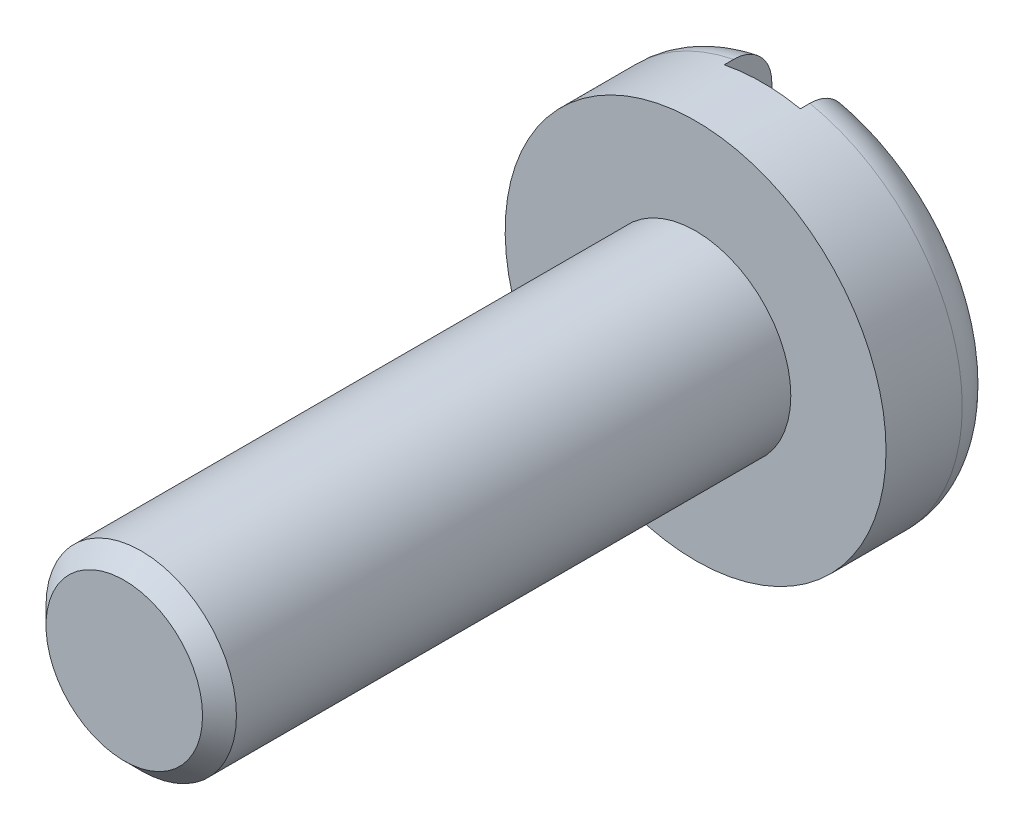
SolidWorks part; units mm, degrees
material "Сталь"
ref_plane "Спереди" through (0, 0, 0) normal (0, 0, 1) x (1, 0, 0)
ref_plane "Сверху" through (0, 0, 0) normal (0, 1, 0) x (1, 0, 0)
ref_plane "Справа" through (0, 0, 0) normal (1, 0, 0) x (0, 0, -1)
sketch "Эскиз1" plane through (0, 0, 0) normal (0, 0, 1) x (1, 0, 0)
  circle A0 centre (0, 0) radius 5
  dimension "D1" = 10
extrude "Бобышка-Вытянуть1" add sketch "Эскиз1" along normal blind 3
sketch "Эскиз2" plane through (0, 0, 3) normal (0, 0, 1) x (1, 0, 0)
  circle A0 centre (0, 0) radius 2.5
  dimension "D1" = 5
extrude "Бобышка-Вытянуть2" add sketch "Эскиз2" along normal blind 15
cosmetic thread "Условное изображение резьбы1" parameters "D2"=4.11
fillet "Скругление1" radius 1 1 edges at (5, 0, 0)
sketch "Эскиз3" plane through (0, 0, 0) normal (0, 1, 0) x (1, 0, 0)
  line L1 (-1, -1.25) -> (1, -1.25)
  line L2 (-1, -1.25) -> (-1, 1.25)
  line L3 (-1, 1.25) -> (1, 1.25)
  line L4 (1, -1.25) -> (1, 1.25)
  line L5 (-1, -1.25) -> (1, 1.25) construction
  line L6 (-1, 1.25) -> (1, -1.25) construction
  point P0 (0, 0)
  dimension "D1" = 2
  dimension "D2" = 2.5
extrude "Вырез-Вытянуть1" cut sketch "Эскиз3" against normal through all and the other way through all
chamfer "Фаска1" distance 0.445 angle 45 1 edges at (2.5, 0, 18)
